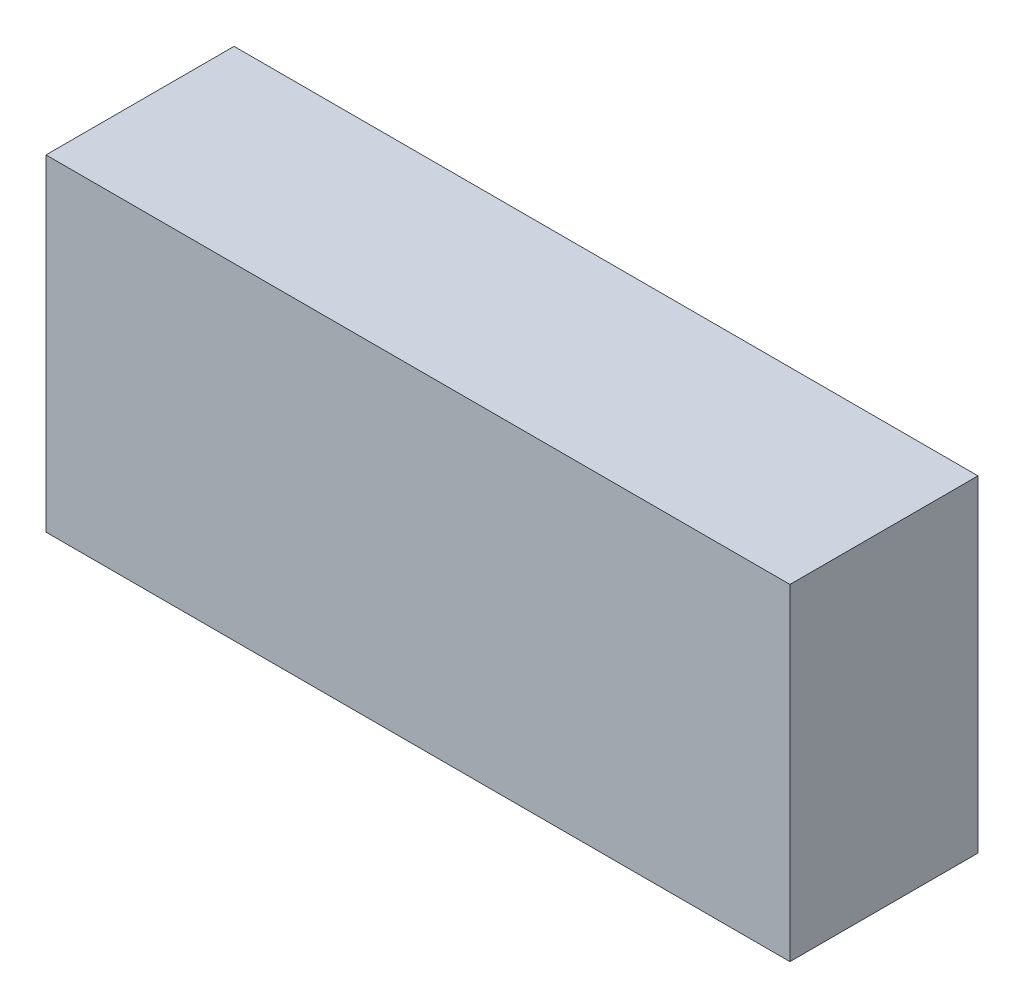
SolidWorks part; units mm, degrees
ref_plane "Front Plane" through (0, 0, 0) normal (0, 0, 1) x (1, 0, 0)
ref_plane "Top Plane" through (0, 0, 0) normal (0, 1, 0) x (1, 0, 0)
ref_plane "Right Plane" through (0, 0, 0) normal (1, 0, 0) x (0, 0, -1)
sketch "Sketch1" plane through (0, 0, 0) normal (0, 0, 1) x (1, 0, 0)
  line L1 (0, 0) -> (55.38, 0)
  line L2 (0, 0) -> (0, 24.32)
  line L3 (0, 24.32) -> (55.38, 24.32)
  line L4 (55.38, 0) -> (55.38, 24.32)
  dimension "D1" = 55.38
  dimension "D2" = 24.32
extrude "Boss-Extrude1" add sketch "Sketch1" along normal blind 14
